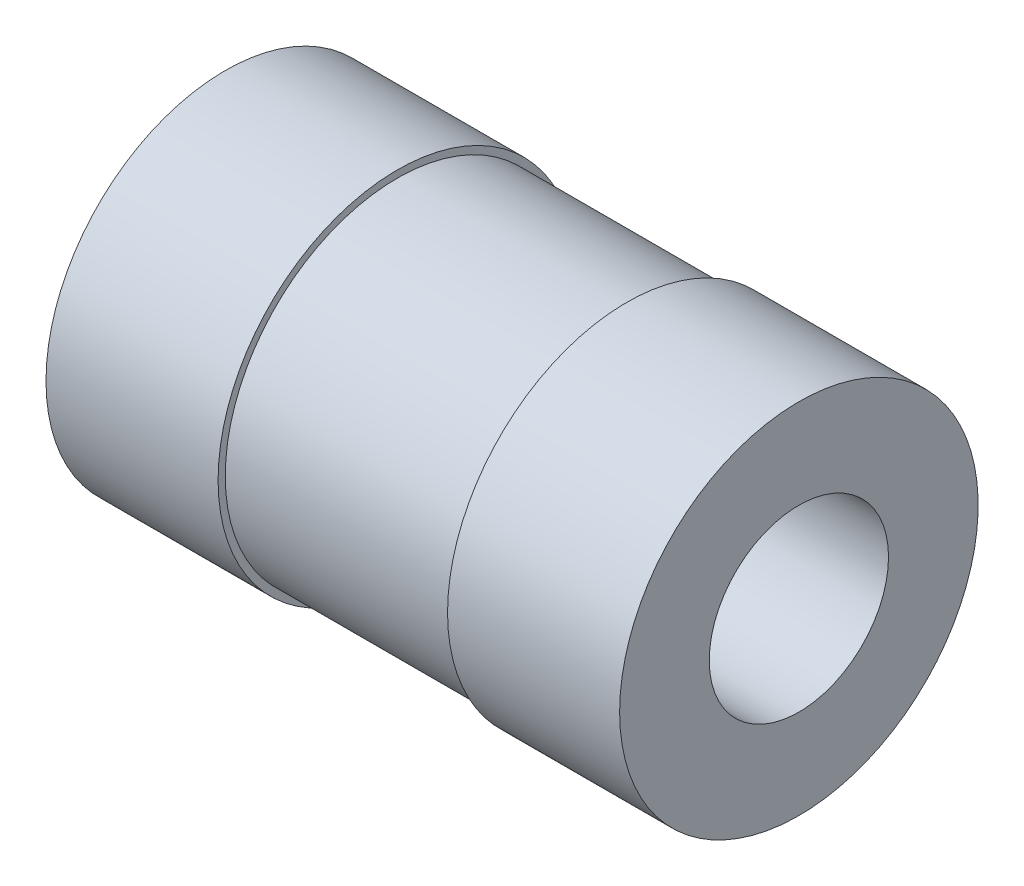
SolidWorks part; units mm, degrees
material "黄铜"
ref_plane "前视基准面" through (0, 0, 0) normal (0, 0, 1) x (1, 0, 0)
ref_plane "上视基准面" through (0, 0, 0) normal (0, 1, 0) x (1, 0, 0)
ref_plane "右视基准面" through (0, 0, 0) normal (1, 0, 0) x (0, 0, -1)
other "Configuration Table"
sketch "草图1" plane through (0, 0, 0) normal (0, 0, 1) x (1, 0, 0)
  line L0 (-2.0226, 0) -> (2.0226, 0) construction
  line L1 (-4, 1.25) -> (4, 1.25)
  line L2 (4, 1.25) -> (4, 2.5)
  line L3 (4, 2.5) -> (1.6, 2.5)
  line L4 (1.6, 2.5) -> (1.6, 2.4)
  line L5 (1.6, 2.4) -> (-1.6, 2.4)
  line L6 (-1.6, 2.4) -> (-1.6, 2.5)
  line L7 (-1.6, 2.5) -> (-4, 2.5)
  line L8 (-4, 2.5) -> (-4, 1.25)
  line L9 (0, 0) -> (0, 1.25) construction
  line L10 (0, 1.25) -> (0, 2.4) construction
  point P4 (0, 0)
  dimension "D1" = 8
  dimension "D2" = 2.5
  dimension "D3" = 5
  dimension "D4" = 2.4
  dimension "D5" = 0.1
revolve "旋转1" add sketch "草图1" angle 360 about L0
cosmetic thread "装饰螺纹线1" parameters "D2"=3.6
equation "\"D4@草图1\"=\"D1@草图1\"*0.3"
